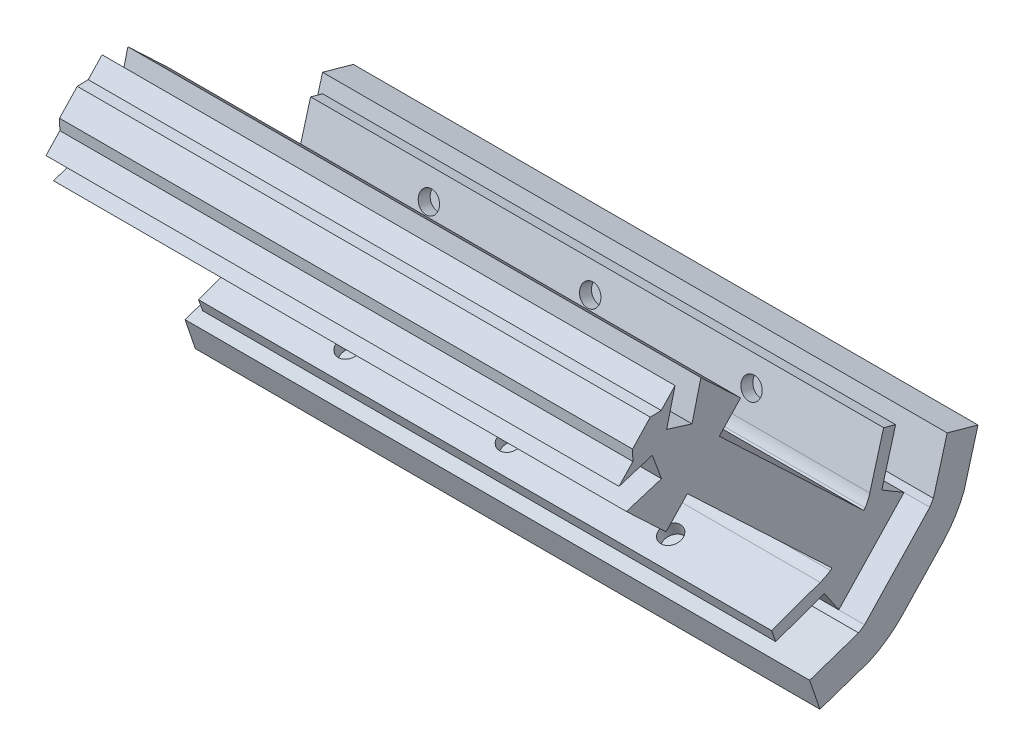
SolidWorks part; units mm, degrees
ref_plane "Alzado" through (0, 0, 0) normal (0, 0, 1) x (1, 0, 0)
ref_plane "Planta" through (0, 0, 0) normal (0, 1, 0) x (1, 0, 0)
ref_plane "Vista lateral" through (0, 0, 0) normal (1, 0, 0) x (0, 0, -1)
sketch "Croquis1" plane through (0, 0, 0) normal (1, 0, 0) x (0, 0, -1)
  line L0 (7.6855, 6.1841) -> (5.1322, 1.8852)
  line L1 (1.961, 5.4899) -> (-4.7709, -1.632)
  line L3 (-1.4049, 1.929) -> (8.0393, -6.998) construction
  line L6 (-2.389, -2.5211) -> (0.4022, -6.6696)
  line L7 (5.1895, 6.8772) -> (2.9828, 3.1618)
  line L8 (10.1816, 5.4909) -> (7.2817, 0.6085)
  line L9 (9.7256, -0.8468) -> (1.9927, -9.0277)
  line L10 (2.8678, 7.5219) -> (16.1485, 3.8339)
  line L12 (-6.7486, -2.6518) -> (-3.1199, -12.7676)
  line L13 (-4.3093, -9.8396) -> (0.4022, -6.6696)
  line L14 (9.835, 4.9074) -> (7.2817, 0.6085) construction
  line L15 (-5.9743, -4.9335) -> (-2.389, -2.5211)
  line L16 (5.5361, 7.4607) -> (2.9828, 3.1618) construction
  line L17 (-5.1418, -7.3865) -> (-0.9934, -4.5954)
  line L18 (2.9828, 3.1618) -> (7.2817, 0.6085)
  line L19 (11.9058, -2.9076) -> (4.1729, -11.0885)
  line L20 (11.9058, -2.9076) -> (4.1729, -11.0885) construction
  line L21 (-6.7486, -2.6518) -> (-2.3191, -15.7039)
  arc A2 (9.7256, -0.8468) -> (13.1719, 4.4682) centre (-2.9922, 11.1744) ccw
  arc A3 (1.961, 5.4899) -> (2.8678, 7.5219) centre (-4.3587, 9.5287) ccw
  arc A5 (-4.7709, -1.632) -> (-6.7486, -2.6518) centre (-9.1589, 4.4504) cw
  arc A6 (1.9927, -9.0277) -> (-3.1199, -12.7676) centre (-10.725, 2.9935) cw
  arc A7 (11.9058, -2.9076) -> (16.1485, 3.8339) centre (-2.9922, 11.1744) ccw
  arc A8 (11.9058, -2.9076) -> (15.9428, 3.3185) centre (-2.9922, 11.1744) ccw construction
  arc A9 (4.1729, -11.0885) -> (-2.3191, -15.7039) centre (-10.725, 2.9935) cw
  point P13 (-4.2545, -7.3148)
  dimension "D2" = 3
  dimension "D3" = 3
  dimension "D5" = 4.9
  dimension "D6" = 5
  dimension "D10" = 6.3345
  dimension "D8" = 2.5
  dimension "D9" = 2.5
extrude "Saliente-Extruir1" add sketch "Croquis1" along normal blind 111
sketch "Croquis2" plane through (0, 7.7228, -2.1446) normal (0, 0.9635, -0.2676) x (1, 0, 0)
  line L4 (0, 14.5339) -> (0, 8.3411)
  line L5 (0, 8.3411) -> (111, 8.3411)
  line L6 (111, 8.3411) -> (111, 14.5339)
  line L7 (111, 14.5339) -> (0, 14.5339)
  line L8 (0, 14.5339) -> (0, 8.3411)
  line L9 (0, 8.3411) -> (111, 8.3411)
  line L10 (111, 8.3411) -> (111, 14.5339)
  line L12 (111, 14.5339) -> (0, 14.5339)
  dimension "D1" = 0
extrude "Saliente-Extruir2" add sketch "Croquis2" along normal blind 10
sketch "Croquis3" plane through (0, 7.7228, -2.1446) normal (0, 0.9635, -0.2676) x (1, 0, 0)
  line L4 (0, 3.1601) -> (0, 0.7506)
  line L5 (0, 0.7506) -> (111, 0.7506)
  line L6 (111, 0.7506) -> (111, 3.1601)
  line L7 (111, 3.1601) -> (0, 3.1601)
  line L8 (0, 3.1601) -> (0, 0.7506)
  line L9 (0, 0.7506) -> (111, 0.7506)
  line L10 (111, 0.7506) -> (111, 3.1601)
  line L11 (111, 3.1601) -> (0, 3.1601)
  dimension "D1" = 0
extrude "Saliente-Extruir3" add sketch "Croquis3" along normal blind 10
sketch "Croquis4" plane through (0, -0.571, 7.495) normal (0, 0.3377, -0.9413) x (1, 0, 0)
  line L4 (0, 4.6092) -> (0, 2.2105)
  line L5 (111, 4.6092) -> (0, 4.6092)
  line L6 (111, 2.2105) -> (111, 4.6092)
  line L7 (0, 2.2105) -> (111, 2.2105)
  line L12 (0, 4.6092) -> (0, 2.2105)
  line L13 (111, 4.6092) -> (0, 4.6092)
  line L14 (111, 2.2105) -> (111, 4.6092)
  line L15 (0, 2.2105) -> (111, 2.2105)
  dimension "D1" = 0
extrude "Saliente-Extruir4" add sketch "Croquis4" against normal blind 10
sketch "Croquis5" plane through (0, -0.4401, 7.4992) normal (0, 0.3214, -0.947) x (1, 0, 0)
  line L4 (0, 16.1188) -> (0, 9.926)
  line L5 (111, 16.1188) -> (0, 16.1188)
  line L6 (111, 9.926) -> (111, 16.1188)
  line L7 (0, 9.926) -> (111, 9.926)
  line L16 (0, 16.1188) -> (0, 9.926)
  line L17 (111, 16.1188) -> (0, 16.1188)
  line L18 (111, 9.926) -> (111, 16.1188)
  line L19 (0, 9.926) -> (111, 9.926)
  dimension "D1" = 0
extrude "Saliente-Extruir5" add sketch "Croquis5" against normal blind 10
sketch "Croquis6" plane through (0, 3.6469, -2.1661) normal (0, 0.8598, -0.5107) x (1, 0, 0)
  line L4 (0, 5.9499) -> (0, 0.9499)
  line L5 (0, 0.9499) -> (111, 0.9499)
  line L6 (111, 0.9499) -> (111, 5.9499)
  line L7 (111, 5.9499) -> (0, 5.9499)
  line L8 (0, 5.9499) -> (0, 0.9499)
  line L9 (0, 0.9499) -> (111, 0.9499)
  line L10 (111, 0.9499) -> (111, 5.9499)
  line L11 (111, 5.9499) -> (0, 5.9499)
  dimension "D1" = 0
extrude "Saliente-Extruir6" add sketch "Croquis6" along normal up to vertex (4.3213 mm away) up to point (0, 6.8772, -5.1895)
sketch "Croquis7" plane through (0, 6.513, 8.4674) normal (0, 0.5582, -0.8297) x (1, 0, 0)
  line L4 (0, 15.8886) -> (0, 10.8886)
  line L5 (111, 15.8886) -> (0, 15.8886)
  line L6 (111, 10.8886) -> (111, 15.8886)
  line L7 (0, 10.8886) -> (111, 10.8886)
  line L12 (0, 15.8886) -> (0, 10.8886)
  line L13 (111, 15.8886) -> (0, 15.8886)
  line L14 (111, 10.8886) -> (111, 15.8886)
  line L15 (0, 10.8886) -> (111, 10.8886)
  dimension "D1" = 0
extrude "Saliente-Extruir7" add sketch "Croquis7" against normal up to vertex (4.2784 mm away) up to point (0, -4.9095, 5.9387)
sketch "Croquis8" plane through (0, 1.6116, 1.705) normal (0, 0.6869, 0.7267) x (1, 0, 0)
  line L0 (111, 0.4368) -> (0, 0.4368) construction
  line L1 (111, 5.3368) -> (111, -4.4632) construction
  line L2 (0, 5.3368) -> (0, -4.4632) construction
  line L4 (111, -4.0632) -> (0, -4.0632)
  line L5 (111, -4.0632) -> (111, 4.9368)
  line L6 (111, 4.9368) -> (0, 4.9368)
  line L7 (0, -4.0632) -> (0, 4.9368)
  dimension "D1" = 4.5
  dimension "D2" = 4.5
extrude "Saliente-Extruir8" add sketch "Croquis8" along normal blind 55
sketch "Croquis9" plane through (0, -3.8889, -14.0039) normal (0, -0.2676, -0.9635) x (-1, 0, 0)
  line L0 (-111, 13.015) -> (0, 13.015) construction
  line L1 (-111, 18.015) -> (-111, 8.015) construction
  line L2 (0, 18.015) -> (0, 8.015) construction
  circle A0 centre (-86.75, 13.015) radius 2
  circle A1 centre (-55.5, 13.015) radius 2
  circle A2 centre (-24.25, 13.015) radius 2
  dimension "D1" = 4
  dimension "D2" = 4
  dimension "D3" = 31.25
  dimension "D4" = 31.25
extrude "Cortar-Extruir1" cut sketch "Croquis9" against normal blind 16
sketch "Croquis10" plane through (0, -3.8889, -14.0039) normal (0, -0.2676, -0.9635) x (-1, 0, 0)
  circle A0 centre (-86.75, 13.015) radius 4
  circle A1 centre (-55.5, 13.015) radius 4
  circle A2 centre (-24.25, 13.015) radius 4
  dimension "D1" = 8
extrude "Cortar-Extruir2" cut sketch "Croquis10" against normal blind 4
sketch "Croquis11" plane through (0, -13.3763, -4.5395) normal (0, -0.947, -0.3214) x (1, 0, 0)
  line L0 (0, 12.2428) -> (111, 12.2428) construction
  line L1 (0, 17.2428) -> (0, 7.2428) construction
  line L2 (111, 17.2428) -> (111, 7.2428) construction
  circle A0 centre (55.5, 12.2428) radius 2
  circle A1 centre (24.25, 12.2428) radius 2
  circle A2 centre (86.75, 12.2428) radius 2
  dimension "D1" = 4
  dimension "D2" = 31.25
  dimension "D3" = 31.25
extrude "Cortar-Extruir3" cut sketch "Croquis11" against normal blind 15
sketch "Croquis12" plane through (0, -13.3763, -4.5395) normal (0, -0.947, -0.3214) x (-1, 0, 0)
  circle A0 centre (-24.25, -12.2428) radius 4
  circle A1 centre (-55.5, -12.2428) radius 4
  circle A2 centre (-86.75, -12.2428) radius 4
  dimension "D1" = 8
extrude "Cortar-Extruir4" cut sketch "Croquis12" against normal blind 4
sketch "Croquis13" plane through (0, 0, 0) normal (-1, 0, 0) x (0, 0, 1)
  line L0 (-9.4884, 4.3239) -> (3.1475, -9.0579)
  line L22 (4.3093, -9.8396) -> (3.1475, -9.0579)
  line L23 (3.1475, -9.0579) -> (5.9387, -4.9095)
  line L24 (5.9387, -4.9095) -> (15.3514, -8.286)
  line L25 (15.3514, -8.286) -> (16.1613, -6.0283)
  line L26 (16.1613, -6.0283) -> (6.7486, -2.6518)
  line L27 (4.7709, -1.632) -> (4.4961, -1.3413)
  line L28 (4.4961, -1.3413) -> (44.4662, 36.4395)
  line L29 (44.4662, 36.4395) -> (38.2839, 42.9801)
  line L30 (38.2839, 42.9801) -> (-1.6862, 5.1993)
  line L31 (-1.6862, 5.1993) -> (-1.961, 5.4899)
  line L32 (-2.8678, 7.5219) -> (-5.5436, 17.1573)
  line L33 (-5.5436, 17.1573) -> (-7.8652, 16.5126)
  line L34 (-7.8652, 16.5126) -> (-5.1895, 6.8772)
  line L35 (-5.1895, 6.8772) -> (-9.4884, 4.3239)
  line L36 (-9.4884, 4.3239) -> (-10.1816, 5.4909)
  line L37 (-10.1816, 5.4909) -> (-12.8573, 15.1263)
  line L38 (-12.8573, 15.1263) -> (-18.8243, 13.4693)
  line L39 (-18.8243, 13.4693) -> (-16.1485, 3.8339)
  line L40 (-11.9058, -2.9076) -> (-4.1729, -11.0885)
  line L41 (2.3191, -15.7039) -> (11.7887, -18.9175)
  line L42 (11.7887, -18.9175) -> (13.7788, -13.0533)
  line L43 (13.7788, -13.0533) -> (4.3093, -9.8396)
  line L44 (4.3093, -9.8396) -> (3.1475, -9.0579)
  line L45 (3.1475, -9.0579) -> (5.9387, -4.9095)
  line L46 (5.9387, -4.9095) -> (15.3514, -8.286)
  line L47 (15.3514, -8.286) -> (16.1613, -6.0283)
  line L48 (16.1613, -6.0283) -> (6.7486, -2.6518)
  line L49 (4.7709, -1.632) -> (4.4961, -1.3413)
  line L50 (4.4961, -1.3413) -> (44.4662, 36.4395)
  line L51 (44.4662, 36.4395) -> (38.2839, 42.9801)
  line L52 (38.2839, 42.9801) -> (-1.6862, 5.1993)
  line L53 (-1.6862, 5.1993) -> (-1.961, 5.4899)
  line L54 (-2.8678, 7.5219) -> (-5.5436, 17.1573)
  line L55 (-5.5436, 17.1573) -> (-7.8652, 16.5126)
  line L56 (-7.8652, 16.5126) -> (-5.1895, 6.8772)
  line L57 (-5.1895, 6.8772) -> (-9.4884, 4.3239)
  line L58 (-9.4884, 4.3239) -> (-10.1816, 5.4909)
  line L59 (-10.1816, 5.4909) -> (-12.8573, 15.1263)
  line L60 (-12.8573, 15.1263) -> (-18.8243, 13.4693)
  line L61 (-18.8243, 13.4693) -> (-16.1485, 3.8339)
  line L62 (-11.9058, -2.9076) -> (-4.1729, -11.0885)
  line L63 (2.3191, -15.7039) -> (11.7887, -18.9175)
  line L64 (11.7887, -18.9175) -> (13.7788, -13.0533)
  line L65 (13.7788, -13.0533) -> (4.3093, -9.8396)
  arc A4 (4.7709, -1.632) -> (6.7486, -2.6518) centre (9.1589, 4.4504) ccw
  arc A5 (-2.8678, 7.5219) -> (-1.961, 5.4899) centre (4.3587, 9.5287) ccw
  arc A6 (-16.1485, 3.8339) -> (-11.9058, -2.9076) centre (2.9922, 11.1744) ccw
  arc A7 (-4.1729, -11.0885) -> (2.3191, -15.7039) centre (10.725, 2.9935) ccw
  arc A8 (4.7709, -1.632) -> (6.7486, -2.6518) centre (9.1589, 4.4504) ccw
  arc A9 (-2.8678, 7.5219) -> (-1.961, 5.4899) centre (4.3587, 9.5287) ccw
  arc A10 (-16.1485, 3.8339) -> (-11.9058, -2.9076) centre (2.9922, 11.1744) ccw
  arc A11 (-4.1729, -11.0885) -> (2.3191, -15.7039) centre (10.725, 2.9935) ccw
  line M27 (4.3093, -9.8396) -> (3.1475, -9.0579)
  line M43 (-9.4884, 4.3239) -> (-10.1816, 5.4909)
  line M44 (-10.1816, 5.4909) -> (-12.8573, 15.1263)
  line M45 (-12.8573, 15.1263) -> (-18.8243, 13.4693)
  line M46 (-18.8243, 13.4693) -> (-16.1485, 3.8339)
  arc M47 (-16.1485, 3.8339) -> (-11.9058, -2.9076) centre (2.9922, 11.1744) ccw
  line M48 (-11.9058, -2.9076) -> (-4.1729, -11.0885)
  arc M49 (-4.1729, -11.0885) -> (2.3191, -15.7039) centre (10.725, 2.9935) ccw
  line M50 (2.3191, -15.7039) -> (11.7887, -18.9175)
  line M51 (11.7887, -18.9175) -> (13.7788, -13.0533)
  line M52 (13.7788, -13.0533) -> (4.3093, -9.8396)
  dimension "D1" = 0
extrude "Saliente-Extruir9" add sketch "Croquis13" along normal blind 5 contours L0 M43 M44 M45 M46 M47 M48 M49 M50 M51 M52 M27
sketch "Croquis14" plane through (-5, 0, 0) normal (-1, 0, 0) x (0, 0, 1)
  line L0 (-5.1895, 6.8772) -> (-9.4884, 4.3239) construction
  line L1 (-9.4884, 4.3239) -> (3.1475, -9.0579) construction
  line L2 (3.1475, -9.0579) -> (5.9387, -4.9095) construction
  line L3 (5.9387, -4.9095) -> (15.3514, -8.286) construction
  line L4 (15.3514, -8.286) -> (16.1613, -6.0283) construction
  line L5 (16.1613, -6.0283) -> (6.7486, -2.6518) construction
  line L6 (4.7709, -1.632) -> (4.4961, -1.3413) construction
  line L7 (4.4961, -1.3413) -> (44.4662, 36.4395) construction
  line L8 (44.4662, 36.4395) -> (38.2839, 42.9801) construction
  line L9 (38.2839, 42.9801) -> (-1.6862, 5.1993) construction
  line L10 (-1.6862, 5.1993) -> (-1.961, 5.4899) construction
  line L11 (-2.8678, 7.5219) -> (-5.5436, 17.1573) construction
  line L12 (-5.5436, 17.1573) -> (-7.8652, 16.5126) construction
  line L13 (-7.8652, 16.5126) -> (-5.1895, 6.8772) construction
  line L14 (3.1475, -9.0579) -> (-9.4884, 4.3239) construction
  line L15 (-9.4884, 4.3239) -> (-10.1816, 5.4909) construction
  line L16 (-10.1816, 5.4909) -> (-12.8573, 15.1263) construction
  line L17 (-12.8573, 15.1263) -> (-18.8243, 13.4693) construction
  line L18 (-18.8243, 13.4693) -> (-16.1485, 3.8339) construction
  line L19 (-11.9058, -2.9076) -> (-4.1729, -11.0885) construction
  line L20 (2.3191, -15.7039) -> (11.7887, -18.9175) construction
  line L21 (11.7887, -18.9175) -> (13.7788, -13.0533) construction
  line L22 (13.7788, -13.0533) -> (4.3093, -9.8396) construction
  line L23 (4.3093, -9.8396) -> (3.1475, -9.0579) construction
  line L24 (-5.1895, 6.8772) -> (-9.4884, 4.3239)
  line L25 (-9.4884, 4.3239) -> (3.1475, -9.0579)
  line L26 (3.1475, -9.0579) -> (5.9387, -4.9095)
  line L27 (5.9387, -4.9095) -> (15.3514, -8.286)
  line L28 (15.3514, -8.286) -> (16.1613, -6.0283)
  line L29 (16.1613, -6.0283) -> (6.7486, -2.6518)
  line L30 (4.7709, -1.632) -> (4.4961, -1.3413)
  line L31 (4.4961, -1.3413) -> (44.4662, 36.4395)
  line L32 (44.4662, 36.4395) -> (38.2839, 42.9801)
  line L33 (38.2839, 42.9801) -> (-1.6862, 5.1993)
  line L34 (-1.6862, 5.1993) -> (-1.961, 5.4899)
  line L35 (-2.8678, 7.5219) -> (-5.5436, 17.1573)
  line L36 (-5.5436, 17.1573) -> (-7.8652, 16.5126)
  line L37 (-7.8652, 16.5126) -> (-5.1895, 6.8772)
  line L38 (3.1475, -9.0579) -> (-9.4884, 4.3239)
  line L39 (-9.4884, 4.3239) -> (-10.1816, 5.4909)
  line L40 (-10.1816, 5.4909) -> (-12.8573, 15.1263)
  line L41 (-12.8573, 15.1263) -> (-18.8243, 13.4693)
  line L42 (-18.8243, 13.4693) -> (-16.1485, 3.8339)
  line L43 (-11.9058, -2.9076) -> (-4.1729, -11.0885)
  line L44 (2.3191, -15.7039) -> (11.7887, -18.9175)
  line L45 (11.7887, -18.9175) -> (13.7788, -13.0533)
  line L46 (13.7788, -13.0533) -> (4.3093, -9.8396)
  line L47 (4.3093, -9.8396) -> (3.1475, -9.0579)
  line L48 (-7.8652, 16.5126) -> (-12.8573, 15.1263)
  line L49 (15.3514, -8.286) -> (13.7788, -13.0533)
  line L50 (4.4961, -1.3413) -> (-1.6862, 5.1993)
  arc A0 (4.7709, -1.632) -> (6.7486, -2.6518) centre (9.1589, 4.4504) ccw construction
  arc A1 (-2.8678, 7.5219) -> (-1.961, 5.4899) centre (4.3587, 9.5287) ccw construction
  arc A2 (-16.1485, 3.8339) -> (-11.9058, -2.9076) centre (2.9922, 11.1744) ccw construction
  arc A3 (-4.1729, -11.0885) -> (2.3191, -15.7039) centre (10.725, 2.9935) ccw construction
  arc A4 (4.7709, -1.632) -> (6.7486, -2.6518) centre (9.1589, 4.4504) ccw
  arc A5 (-2.8678, 7.5219) -> (-1.961, 5.4899) centre (4.3587, 9.5287) ccw
  arc A6 (-16.1485, 3.8339) -> (-11.9058, -2.9076) centre (2.9922, 11.1744) ccw
  arc A7 (-4.1729, -11.0885) -> (2.3191, -15.7039) centre (10.725, 2.9935) ccw
  line M29 (3.1475, -9.0579) -> (-9.4884, 4.3239)
  line M30 (-9.4884, 4.3239) -> (-10.1816, 5.4909)
  line M31 (-10.1816, 5.4909) -> (-12.8573, 15.1263)
  line M32 (-12.8573, 15.1263) -> (-18.8243, 13.4693)
  line M33 (-18.8243, 13.4693) -> (-16.1485, 3.8339)
  arc M34 (-16.1485, 3.8339) -> (-11.9058, -2.9076) centre (2.9922, 11.1744) ccw
  line M35 (-11.9058, -2.9076) -> (-4.1729, -11.0885)
  arc M36 (-4.1729, -11.0885) -> (2.3191, -15.7039) centre (10.725, 2.9935) ccw
  line M37 (2.3191, -15.7039) -> (11.7887, -18.9175)
  line M38 (11.7887, -18.9175) -> (13.7788, -13.0533)
  line M39 (13.7788, -13.0533) -> (4.3093, -9.8396)
  line M40 (4.3093, -9.8396) -> (3.1475, -9.0579)
extrude "Saliente-Extruir10" [suppressed] add sketch "Croquis14" along normal blind 2 contours M40 M29 M30 M31 M32 M33 M34 M35 M36 M37 M38 M39 | A5 L35 L36 L37 L24 L26 L27 L28 L29 A4 L30 L50 L34 M29 | L49 L27 L26 M40 M39 | L37 L48 L24 M31 M30
sketch "Croquis15" plane through (111, 0, 0) normal (1, 0, 0) x (0, 0, -1)
  line L0 (-15.3514, -8.286) -> (-13.7788, -13.0533)
  line L1 (7.8652, 16.5126) -> (12.8573, 15.1263)
  line L2 (1.6862, 5.1993) -> (-4.4961, -1.3413)
  line L3 (-3.1475, -9.0579) -> (9.4884, 4.3239)
  line L22 (-3.1475, -9.0579) -> (-4.3093, -9.8396)
  line L23 (-4.3093, -9.8396) -> (-13.7788, -13.0533)
  line L24 (-13.7788, -13.0533) -> (-11.7887, -18.9175)
  line L25 (-11.7887, -18.9175) -> (-2.3191, -15.7039)
  line L26 (4.1729, -11.0885) -> (11.9058, -2.9076)
  line L27 (16.1485, 3.8339) -> (18.8243, 13.4693)
  line L28 (18.8243, 13.4693) -> (12.8573, 15.1263)
  line L29 (12.8573, 15.1263) -> (10.1816, 5.4909)
  line L30 (10.1816, 5.4909) -> (9.4884, 4.3239)
  line L31 (9.4884, 4.3239) -> (5.1895, 6.8772)
  line L32 (5.1895, 6.8772) -> (7.8652, 16.5126)
  line L33 (7.8652, 16.5126) -> (5.5436, 17.1573)
  line L34 (5.5436, 17.1573) -> (2.8678, 7.5219)
  line L35 (1.961, 5.4899) -> (1.6862, 5.1993)
  line L36 (1.6862, 5.1993) -> (-38.2839, 42.9801)
  line L37 (-38.2839, 42.9801) -> (-44.4662, 36.4395)
  line L38 (-44.4662, 36.4395) -> (-4.4961, -1.3413)
  line L39 (-4.4961, -1.3413) -> (-4.7709, -1.632)
  line L40 (-6.7486, -2.6518) -> (-16.1613, -6.0283)
  line L41 (-16.1613, -6.0283) -> (-15.3514, -8.286)
  line L42 (-15.3514, -8.286) -> (-5.9387, -4.9095)
  line L43 (-5.9387, -4.9095) -> (-3.1475, -9.0579)
  line L44 (-3.1475, -9.0579) -> (-4.3093, -9.8396)
  line L45 (-4.3093, -9.8396) -> (-13.7788, -13.0533)
  line L46 (-13.7788, -13.0533) -> (-11.7887, -18.9175)
  line L47 (-11.7887, -18.9175) -> (-2.3191, -15.7039)
  line L48 (4.1729, -11.0885) -> (11.9058, -2.9076)
  line L49 (16.1485, 3.8339) -> (18.8243, 13.4693)
  line L50 (18.8243, 13.4693) -> (12.8573, 15.1263)
  line L51 (12.8573, 15.1263) -> (10.1816, 5.4909)
  line L52 (10.1816, 5.4909) -> (9.4884, 4.3239)
  line L53 (9.4884, 4.3239) -> (5.1895, 6.8772)
  line L54 (5.1895, 6.8772) -> (7.8652, 16.5126)
  line L55 (7.8652, 16.5126) -> (5.5436, 17.1573)
  line L56 (5.5436, 17.1573) -> (2.8678, 7.5219)
  line L57 (1.961, 5.4899) -> (1.6862, 5.1993)
  line L58 (1.6862, 5.1993) -> (-38.2839, 42.9801)
  line L59 (-38.2839, 42.9801) -> (-44.4662, 36.4395)
  line L60 (-44.4662, 36.4395) -> (-4.4961, -1.3413)
  line L61 (-4.4961, -1.3413) -> (-4.7709, -1.632)
  line L62 (-6.7486, -2.6518) -> (-16.1613, -6.0283)
  line L63 (-16.1613, -6.0283) -> (-15.3514, -8.286)
  line L64 (-15.3514, -8.286) -> (-5.9387, -4.9095)
  line L65 (-5.9387, -4.9095) -> (-3.1475, -9.0579)
  arc A4 (-2.3191, -15.7039) -> (4.1729, -11.0885) centre (-10.725, 2.9935) ccw
  arc A5 (11.9058, -2.9076) -> (16.1485, 3.8339) centre (-2.9922, 11.1744) ccw
  arc A6 (1.961, 5.4899) -> (2.8678, 7.5219) centre (-4.3587, 9.5287) ccw
  arc A7 (-6.7486, -2.6518) -> (-4.7709, -1.632) centre (-9.1589, 4.4504) ccw
  arc A8 (-2.3191, -15.7039) -> (4.1729, -11.0885) centre (-10.725, 2.9935) ccw
  arc A9 (11.9058, -2.9076) -> (16.1485, 3.8339) centre (-2.9922, 11.1744) ccw
  arc A10 (1.961, 5.4899) -> (2.8678, 7.5219) centre (-4.3587, 9.5287) ccw
  arc A11 (-6.7486, -2.6518) -> (-4.7709, -1.632) centre (-9.1589, 4.4504) ccw
  line M27 (-3.1475, -9.0579) -> (-4.3093, -9.8396)
  line M28 (-4.3093, -9.8396) -> (-13.7788, -13.0533)
  line M29 (-13.7788, -13.0533) -> (-11.7887, -18.9175)
  line M30 (-11.7887, -18.9175) -> (-2.3191, -15.7039)
  arc M31 (-2.3191, -15.7039) -> (4.1729, -11.0885) centre (-10.725, 2.9935) ccw
  line M32 (4.1729, -11.0885) -> (11.9058, -2.9076)
  arc M33 (11.9058, -2.9076) -> (16.1485, 3.8339) centre (-2.9922, 11.1744) ccw
  line M34 (16.1485, 3.8339) -> (18.8243, 13.4693)
  line M35 (18.8243, 13.4693) -> (12.8573, 15.1263)
  line M36 (12.8573, 15.1263) -> (10.1816, 5.4909)
  line M37 (10.1816, 5.4909) -> (9.4884, 4.3239)
  dimension "D1" = 0
extrude "Saliente-Extruir11" add sketch "Croquis15" along normal blind 5 contours L3 M27 M28 M29 M30 M31 M32 M33 M34 M35 M36 M37
sketch "Croquis16" plane through (116, 0, 0) normal (1, 0, 0) x (0, 0, -1)
  line L10 (9.4884, 4.3239) -> (-3.1475, -9.0579)
  line L11 (-3.1475, -9.0579) -> (-4.3093, -9.8396)
  line L12 (-4.3093, -9.8396) -> (-13.7788, -13.0533)
  line L13 (-13.7788, -13.0533) -> (-11.7887, -18.9175)
  line L14 (-11.7887, -18.9175) -> (-2.3191, -15.7039)
  line L15 (4.1729, -11.0885) -> (11.9058, -2.9076)
  line L16 (16.1485, 3.8339) -> (18.8243, 13.4693)
  line L17 (18.8243, 13.4693) -> (12.8573, 15.1263)
  line L18 (12.8573, 15.1263) -> (10.1816, 5.4909)
  line L19 (10.1816, 5.4909) -> (9.4884, 4.3239)
  line L20 (9.4884, 4.3239) -> (-3.1475, -9.0579)
  line L21 (-3.1475, -9.0579) -> (-4.3093, -9.8396)
  line L22 (-4.3093, -9.8396) -> (-13.7788, -13.0533)
  line L23 (-13.7788, -13.0533) -> (-11.7887, -18.9175)
  line L24 (-11.7887, -18.9175) -> (-2.3191, -15.7039)
  line L25 (4.1729, -11.0885) -> (11.9058, -2.9076)
  line L26 (16.1485, 3.8339) -> (18.8243, 13.4693)
  line L27 (18.8243, 13.4693) -> (12.8573, 15.1263)
  line L28 (12.8573, 15.1263) -> (10.1816, 5.4909)
  line L29 (10.1816, 5.4909) -> (9.4884, 4.3239)
  line L34 (-15.3514, -8.286) -> (-13.7788, -13.0533)
  line L35 (7.8652, 16.5126) -> (12.8573, 15.1263)
  line L36 (1.6862, 5.1993) -> (-4.4961, -1.3413)
  line L48 (-5.9387, -4.9095) -> (-3.1475, -9.0579)
  line L49 (-3.1475, -9.0579) -> (9.4884, 4.3239)
  line L50 (9.4884, 4.3239) -> (5.1895, 6.8772)
  line L51 (5.1895, 6.8772) -> (7.8652, 16.5126)
  line L52 (7.8652, 16.5126) -> (5.5436, 17.1573)
  line L53 (5.5436, 17.1573) -> (2.8678, 7.5219)
  line L54 (1.961, 5.4899) -> (1.6862, 5.1993)
  line L55 (1.6862, 5.1993) -> (-38.2839, 42.9801)
  line L56 (-38.2839, 42.9801) -> (-44.4662, 36.4395)
  line L57 (-44.4662, 36.4395) -> (-4.4961, -1.3413)
  line L58 (-4.4961, -1.3413) -> (-4.7709, -1.632)
  line L59 (-6.7486, -2.6518) -> (-16.1613, -6.0283)
  line L60 (-16.1613, -6.0283) -> (-15.3514, -8.286)
  line L61 (-15.3514, -8.286) -> (-5.9387, -4.9095)
  line L62 (-5.9387, -4.9095) -> (-3.1475, -9.0579)
  line L63 (-3.1475, -9.0579) -> (9.4884, 4.3239)
  line L64 (9.4884, 4.3239) -> (5.1895, 6.8772)
  line L65 (5.1895, 6.8772) -> (7.8652, 16.5126)
  line L66 (7.8652, 16.5126) -> (5.5436, 17.1573)
  line L67 (5.5436, 17.1573) -> (2.8678, 7.5219)
  line L68 (1.961, 5.4899) -> (1.6862, 5.1993)
  line L69 (1.6862, 5.1993) -> (-38.2839, 42.9801)
  line L70 (-38.2839, 42.9801) -> (-44.4662, 36.4395)
  line L71 (-44.4662, 36.4395) -> (-4.4961, -1.3413)
  line L72 (-4.4961, -1.3413) -> (-4.7709, -1.632)
  line L73 (-6.7486, -2.6518) -> (-16.1613, -6.0283)
  line L74 (-16.1613, -6.0283) -> (-15.3514, -8.286)
  line L75 (-15.3514, -8.286) -> (-5.9387, -4.9095)
  arc A2 (-2.3191, -15.7039) -> (4.1729, -11.0885) centre (-10.725, 2.9935) ccw
  arc A3 (11.9058, -2.9076) -> (16.1485, 3.8339) centre (-2.9922, 11.1744) ccw
  arc A4 (-2.3191, -15.7039) -> (4.1729, -11.0885) centre (-10.725, 2.9935) ccw
  arc A5 (11.9058, -2.9076) -> (16.1485, 3.8339) centre (-2.9922, 11.1744) ccw
  arc A8 (1.961, 5.4899) -> (2.8678, 7.5219) centre (-4.3587, 9.5287) ccw
  arc A9 (-6.7486, -2.6518) -> (-4.7709, -1.632) centre (-9.1589, 4.4504) ccw
  arc A10 (1.961, 5.4899) -> (2.8678, 7.5219) centre (-4.3587, 9.5287) ccw
  arc A11 (-6.7486, -2.6518) -> (-4.7709, -1.632) centre (-9.1589, 4.4504) ccw
  line M29 (9.4884, 4.3239) -> (-3.1475, -9.0579)
  line M30 (-3.1475, -9.0579) -> (-4.3093, -9.8396)
  line M31 (-4.3093, -9.8396) -> (-13.7788, -13.0533)
  line M32 (-13.7788, -13.0533) -> (-11.7887, -18.9175)
  line M33 (-11.7887, -18.9175) -> (-2.3191, -15.7039)
  arc M34 (-2.3191, -15.7039) -> (4.1729, -11.0885) centre (-10.725, 2.9935) ccw
  line M35 (4.1729, -11.0885) -> (11.9058, -2.9076)
  arc M36 (11.9058, -2.9076) -> (16.1485, 3.8339) centre (-2.9922, 11.1744) ccw
  line M37 (16.1485, 3.8339) -> (18.8243, 13.4693)
  line M38 (18.8243, 13.4693) -> (12.8573, 15.1263)
  line M39 (12.8573, 15.1263) -> (10.1816, 5.4909)
  line M40 (10.1816, 5.4909) -> (9.4884, 4.3239)
  dimension "D1" = 0
  dimension "D2" = 0
extrude "Saliente-Extruir12" [suppressed] add sketch "Croquis16" along normal blind 2 contours M40 M29 M30 M31 M32 M33 M34 M35 M36 M37 M38 M39 | A11 L73 L74 L75 L62 L64 L65 L66 L67 A10 L68 L36 L72 M29 | L65 L64 L35 M40 M39 | L75 L34 L62 M31 M30
chamfer "Chaflán1" distance 2 angle 45 2 edges at (55.5, 36.4395, 44.4662) (55.5, 42.9801, 38.2839)
sketch "Croquis17" plane through (0, 3.5877, -3.3912) normal (0, 0.7267, -0.6869) x (1, 0, 0)
  line L0 (0, -55.3461) -> (0, -2.3461) construction
  line L1 (0, -53.3461) -> (111, -53.3461)
  line L2 (0, -53.3461) -> (0, -55.8461)
  line L3 (0, -55.8461) -> (111, -55.8461)
  line L4 (111, -53.3461) -> (111, -55.8461)
  line L5 (111, -55.3461) -> (111, -57.3461) construction
  line L6 (0, -55.3461) -> (111, -55.3461) construction
  dimension "D1" = 0.5
  dimension "D2" = 2
extrude "Cortar-Extruir5" cut sketch "Croquis17" against normal blind 1
sketch "Croquis18" plane through (0, -2.9529, 2.7911) normal (0, -0.7267, 0.6869) x (-1, 0, 0)
  line L0 (0, -55.3461) -> (0, -2.3461) construction
  line L1 (0, -53.3461) -> (-111, -53.3461)
  line L2 (0, -53.3461) -> (0, -55.8461)
  line L3 (0, -55.8461) -> (-111, -55.8461)
  line L4 (-111, -53.3461) -> (-111, -55.8461)
  line L5 (-111, -57.3461) -> (-111, -55.3461) construction
  line L6 (-111, -55.3461) -> (0, -55.3461) construction
  dimension "D1" = 0.5
  dimension "D2" = 2
extrude "Cortar-Extruir6" cut sketch "Croquis18" against normal blind 1
sketch "Croquis19" plane through (0, 0, 0) normal (-1, 0, 0) x (0, 0, 1)
  line L0 (37.5372, 41.5864) -> (33.0722, 46.3101)
  line L1 (33.0722, 46.3101) -> (22.1713, 36.0062)
  line L2 (22.1713, 36.0062) -> (36.5967, 20.7449)
  line L3 (36.5967, 20.7449) -> (47.4976, 31.0488)
  line L4 (47.4976, 31.0488) -> (43.0326, 35.7725)
  line L5 (39.6577, 41.5266) -> (43.0923, 37.893) construction
  line L6 (41.5593, 33.6918) -> (4.4961, -1.3413) construction
  line L7 (35.3769, 40.2324) -> (-1.6862, 5.1993) construction
  line L30 (40.8723, 34.4186) -> (42.6892, 36.1359)
  line L31 (42.6892, 36.1359) -> (43.0326, 35.7725)
  line L32 (43.0326, 35.7725) -> (43.0923, 37.893)
  line L33 (43.0923, 37.893) -> (39.6577, 41.5266)
  line L34 (39.6577, 41.5266) -> (37.5372, 41.5864)
  line L35 (37.5372, 41.5864) -> (37.8807, 41.223)
  line L36 (37.8807, 41.223) -> (36.0639, 39.5057)
  line L37 (36.0639, 39.5057) -> (35.3769, 40.2324)
  line L38 (35.3769, 40.2324) -> (-1.6862, 5.1993)
  line L39 (-1.6862, 5.1993) -> (-1.961, 5.4899)
  line L40 (-2.8678, 7.5219) -> (-5.5436, 17.1573)
  line L41 (-5.5436, 17.1573) -> (-7.8652, 16.5126)
  line L42 (-7.8652, 16.5126) -> (-5.1895, 6.8772)
  line L43 (-5.1895, 6.8772) -> (-9.4884, 4.3239)
  line L44 (-9.4884, 4.3239) -> (3.1475, -9.0579)
  line L45 (3.1475, -9.0579) -> (5.9387, -4.9095)
  line L46 (5.9387, -4.9095) -> (15.3514, -8.286)
  line L47 (15.3514, -8.286) -> (16.1613, -6.0283)
  line L48 (16.1613, -6.0283) -> (6.7486, -2.6518)
  line L49 (4.7709, -1.632) -> (4.4961, -1.3413)
  line L50 (4.4961, -1.3413) -> (41.5593, 33.6918)
  line L51 (41.5593, 33.6918) -> (40.8723, 34.4186)
  line L54 (43.0326, 35.7725) -> (43.0923, 37.893)
  line L55 (43.0923, 37.893) -> (39.6577, 41.5266)
  line L56 (39.6577, 41.5266) -> (37.5372, 41.5864)
  arc A2 (-2.8678, 7.5219) -> (-1.961, 5.4899) centre (4.3587, 9.5287) ccw
  arc A3 (4.7709, -1.632) -> (6.7486, -2.6518) centre (9.1589, 4.4504) ccw
  dimension "D1" = 15
  dimension "D2" = 6
  dimension "D3" = 6
  dimension "D4" = 0
extrude "Saliente-Extruir13" add sketch "Croquis19" against normal up to surface (111 mm away) up to face at (111, 17.1272, 17.4859)
sketch "Croquis20" plane through (0, 0, 0) normal (-1, 0, 0) x (0, 0, 1)
  line L0 (45.7135, 32.9363) -> (39.2691, 34.9363)
  line L1 (47.4976, 31.0488) -> (43.0326, 35.7725) construction
  line L2 (39.2691, 34.9363) -> (37.4847, 30.1106)
  line L3 (37.4847, 30.1106) -> (44.2755, 28.0031)
  line L4 (36.5967, 20.7449) -> (47.4976, 31.0488) construction
  line L5 (44.2755, 28.0031) -> (47.4976, 31.0488)
  line L6 (47.4976, 31.0488) -> (45.7135, 32.9363)
  line L7 (41.375, 39.7098) -> (29.3435, 28.3373) construction
  line L8 (43.0923, 37.893) -> (39.6577, 41.5266) construction
  line L9 (33.0722, 46.3101) -> (22.1713, 36.0062) construction
  line L10 (33.0722, 46.3101) -> (34.8564, 44.4226)
  line L11 (29.8501, 43.2644) -> (33.0722, 46.3101)
  line L12 (36.4906, 37.8758) -> (31.5721, 36.3658)
  line L13 (34.8564, 44.4226) -> (36.4906, 37.8758)
  line L14 (31.5721, 36.3658) -> (29.8501, 43.2644)
extrude "Cortar-Extruir7" cut sketch "Croquis20" against normal up to surface (111 mm away) up to face at (111, 15.6961, 15.9719)
